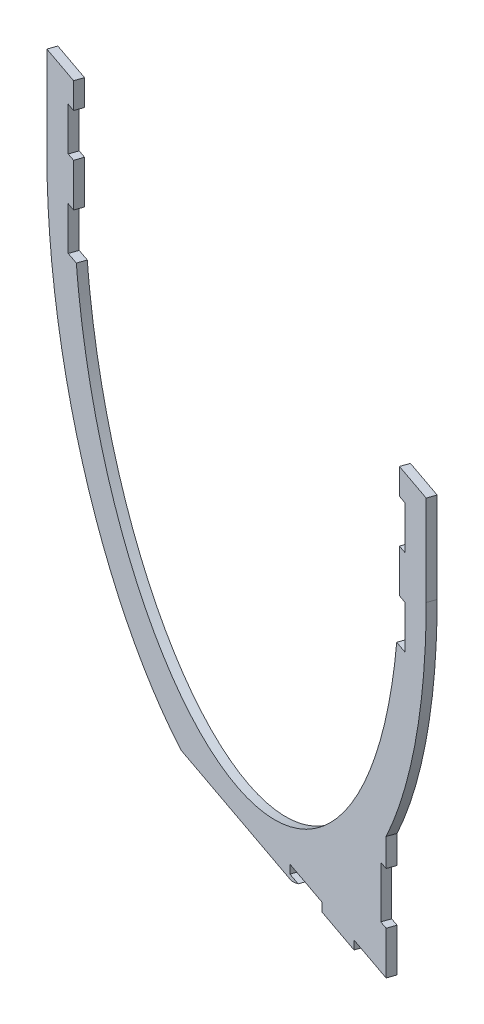
SolidWorks part; units mm, degrees
ref_plane "Front Plane" through (0, 0, 0) normal (0, 0, 1) x (1, 0, 0)
ref_plane "Top Plane" through (0, 0, 0) normal (0, 1, 0) x (1, 0, 0)
ref_plane "Right Plane" through (0, 0, 0) normal (1, 0, 0) x (0, 0, -1)
sketch "Sketch2" plane through (0, 0, 0) normal (0, 1, 0) x (1, 0, 0)
  line L0 (-295.0403, 95.1378) -> (-34.5174, 903.069) construction
  line L1 (-25, 910) -> (25, 910) construction
  line L2 (0, 0) -> (0, 870) construction
  line L3 (-181.6808, 251.1814) -> (-9.5174, 785.0928) construction
  line L4 (295.0403, 95.1378) -> (32.2825, 910) construction
  line L5 (181.6808, 251.1814) -> (9.5174, 785.0928) construction
  line L6 (-250, 0) -> (-250, 956.0819)
  line L7 (-250, 956.0819) -> (250, 783.9181)
  line L8 (-591.5307, 0) -> (570.3863, 0) construction
  line L9 (181.6808, -251.1814) -> (9.5174, -785.0928) construction
  line L10 (295.0403, -95.1378) -> (32.2825, -910) construction
  line L11 (-181.6808, -251.1814) -> (-9.5174, -785.0928) construction
  line L12 (-25, -910) -> (25, -910) construction
  line L13 (-295.0403, -95.1378) -> (-34.5174, -903.069) construction
  line L14 (250, 783.9181) -> (250, 0)
  line L15 (0, 870) -> (-535.6255, 184.4306)
  line L16 (250, 783.9181) -> (-338.6228, 30.5153)
  line L17 (-662.1318, 870) -> (570.3863, 870) construction
  line L18 (-338.6228, 30.5153) -> (-732.6282, 338.346)
  line L19 (-732.6282, 338.346) -> (-250, 956.0819)
  line L20 (0, 870) -> (-283.2443, 47.3988) construction
  circle A0 centre (0, 0) radius 250 construction
  arc A1 (181.6808, 251.1814) -> (-181.6808, 251.1814) centre (0, 0) ccw construction
  arc A2 (-9.5174, 785.0928) -> (9.5174, 785.0928) centre (0, 782.0238) cw construction
  arc A3 (-295.0403, 95.1378) -> (-295.0403, -95.1378) centre (0, 0) ccw construction
  arc A4 (-25, 910) -> (-34.5174, 903.069) centre (-25, 900) ccw construction
  arc A5 (25, 910) -> (34.5174, 903.069) centre (25, 900) cw construction
  arc A6 (0, 0) -> (-535.6255, 184.4306) centre (0, 870) cw construction
  arc A22 (25, -910) -> (34.5174, -903.069) centre (25, -900) ccw construction
  arc A23 (-25, -910) -> (-34.5174, -903.069) centre (-25, -900) cw construction
  arc A24 (-9.5174, -785.0928) -> (9.5174, -785.0928) centre (0, -782.0238) ccw construction
  arc A25 (181.6808, -251.1814) -> (-181.6808, -251.1814) centre (0, 0) cw construction
  arc A26 (-181.6808, -251.1814) -> (181.6808, -251.1814) centre (0, 0) ccw construction
  arc A27 (295.0403, -95.1378) -> (295.0403, 95.1378) centre (0, 0) ccw construction
  point P15 (0, 814.6081)
  point P17 (-32.2825, 910)
  point P21 (0, 910)
  point P69 (0, -910)
  dimension "D1" = 500
  dimension "D2" = 10
  dimension "D3" = 10
  dimension "D4" = 870
  dimension "D5" = 19
  dimension "D8" = 60
  dimension "D9" = 910
  dimension "D11" = 50
ref_plane "Plane1" through (0, 0, -870) normal (0, 0, 1) x (1, 0, 0)
sketch "Sketch3" plane through (0, 0, -870) normal (0, 0, 1) x (1, 0, 0)
  line L0 (0, 0) -> (0, 621.6859) construction
ref_plane "Plane2" through (267.8127, 0, -777.7847) normal (-0.3256, 0, 0.9455) x (0.9455, 0, 0.3256)
ref_plane "Plane3" through (274.3241, 0, -796.695) normal (-0.3256, 0, 0.9455) x (0.9455, 0, 0.3256)
sketch "Sketch4" plane through (274.3241, 0, -796.695) normal (-0.3256, 0, 0.9455) x (0.9455, 0, 0.3256)
  line L0 (-283.2443, 938.347) -> (-283.2443, -30) construction
  line L1 (-761.4579, 410) -> (151.8347, 410) construction
  line L2 (-538.2443, 410) -> (-538.2443, 470) construction
  line L3 (-538.2443, 470) -> (-558.2443, 470) construction
  line L4 (-558.2443, 470) -> (-558.2443, 350) construction
  line L5 (-558.2443, 470) -> (-544.8659, 527.0811) construction
  line L6 (-8.2443, 350) -> (-21.6227, 292.9189) construction
  line L7 (-558.2443, 350) -> (-544.8659, 292.9189) construction
  line L8 (-8.2443, 470) -> (-21.6227, 527.0811) construction
  line L9 (-8.2443, 470) -> (-8.2443, 350) construction
  line L10 (21.7557, 485) -> (21.7557, 515)
  line L11 (-386.784, -30) -> (-179.7046, -30)
  line L12 (21.7557, 515) -> (71.7557, 515)
  line L13 (-118.2838, 5.4462) -> (39.5332, 5.4462) construction
  line L14 (-118.2838, 17.9462) -> (-18.2838, 17.9462) construction
  line L15 (-118.2838, 17.9462) -> (-118.2838, -7.0538) construction
  line L16 (-118.2838, -7.0538) -> (-18.2838, -7.0538) construction
  line L17 (-18.2838, 17.9462) -> (-18.2838, -7.0538) construction
  line L18 (1.7557, 17.9462) -> (6.7557, 17.9462) construction
  line L19 (-63.2443, -15) -> (-3.2443, -15)
  line L20 (-3.2443, 155) -> (-13.2443, 155) construction
  line L21 (21.7557, 335) -> (31.7557, 335)
  line L22 (31.7557, 335) -> (31.7557, 485) construction
  line L23 (31.7557, 485) -> (21.7557, 485)
  line L24 (21.7557, 485) -> (21.7557, 335) construction
  line L25 (-3.2443, 155) -> (-3.2443, -25) construction
  line L26 (71.7557, 515) -> (71.7557, 410)
  line L27 (21.7557, 515) -> (21.7557, 485)
  line L28 (-8.2443, 470) -> (1.7557, 470) construction
  line L29 (1.7557, 470) -> (1.7557, 350) construction
  line L30 (1.7557, 350) -> (-8.2443, 350) construction
  line L31 (1.7557, 470) -> (1.7557, 485) construction
  line L32 (1.7557, 485) -> (6.7557, 485) construction
  line L33 (6.7557, 485) -> (6.7557, -7.0538) construction
  line L34 (1.7557, 350) -> (1.7557, -7.0538) construction
  line L35 (1.7557, -7.0538) -> (6.7557, -7.0538) construction
  line L36 (-3.2443, -25) -> (-13.2443, -25) construction
  line L37 (-13.2443, 155) -> (-13.2443, -25) construction
  line L38 (-183.2443, -15) -> (-3.2443, -15) construction
  line L39 (-183.2443, -15) -> (-183.2443, -25)
  line L40 (-183.2443, -25) -> (-3.2443, -25) construction
  line L41 (-3.2443, -15) -> (-3.2443, -25) construction
  line L42 (-3.2443, 35) -> (-3.2443, -15)
  line L43 (-123.2443, -15) -> (-123.2443, -25)
  line L44 (-63.2443, -25) -> (-63.2443, -15)
  line L45 (-13.2443, 35) -> (-3.2443, 35)
  line L46 (-13.2443, 95) -> (-3.2443, 95)
  line L47 (-3.2443, 95) -> (-3.2443, 127.2211)
  line L48 (-13.2443, 95) -> (-13.2443, 35)
  line L49 (-3.2443, 35) -> (-3.2443, -25) construction
  line L50 (-3.2443, -15) -> (32.7751, -15.846)
  line L51 (-123.2443, -25) -> (-63.2443, -25)
  line L52 (-123.2443, -15) -> (-183.2443, -15)
  line L53 (-183.2443, -25) -> (-167.8054, -25)
  line L54 (31.7557, 435) -> (21.7557, 435)
  line L55 (31.7557, 385) -> (21.7557, 385)
  line L56 (31.7557, 435) -> (31.7557, 485)
  line L57 (21.7557, 435) -> (21.7557, 385)
  line L58 (31.7557, 385) -> (31.7557, 335)
  line L59 (21.7557, 335) -> (16.6093, 335)
  line L60 (-638.2443, 515) -> (-638.2443, 410)
  line L61 (-588.2443, 515) -> (-638.2443, 515)
  line L62 (-598.2443, 485) -> (-588.2443, 485)
  line L63 (-598.2443, 435) -> (-598.2443, 485)
  line L64 (-598.2443, 435) -> (-588.2443, 435)
  line L65 (-598.2443, 385) -> (-588.2443, 385)
  line L66 (-588.2443, 435) -> (-588.2443, 385)
  line L67 (-598.2443, 385) -> (-598.2443, 335)
  line L68 (-588.2443, 335) -> (-583.0979, 335)
  line L69 (-588.2443, 335) -> (-598.2443, 335)
  line L70 (-588.2443, 485) -> (-588.2443, 515)
  ellipse E0 centre (-283.2443, 410) end of major axis (-283.2443, 55) minor radius 250 construction
  ellipse E1 centre (-283.2443, 410) end of major axis (-283.2443, 790) minor radius 275 construction
  ellipse E2 centre (-283.2443, 410) end of major axis (-283.2443, 788.3034) minor radius 275.1297 (-544.8659, 527.0811) -> (-21.6227, 527.0811) cw construction
  ellipse E3 centre (-283.2443, 410) end of major axis (-283.2443, 31.6966) minor radius 275.1297 (-544.8659, 292.9189) -> (-21.6227, 292.9189) ccw construction
  ellipse E4 centre (-283.2443, 410) end of major axis (-283.2443, 0) minor radius 305 (-588.2443, 410) -> (21.7557, 410) ccw construction
  ellipse E5 centre (-283.2443, 410) end of major axis (-283.2443, 870) minor radius 355 (-638.2443, 410) -> (-386.784, -30) ccw
  ellipse E6 centre (-283.2443, 410) end of major axis (-283.2443, -25) minor radius 332.1412 (48.8969, 410) -> (-283.2443, -25) cw construction
  ellipse E7 centre (-283.2443, 410) end of major axis (-283.2443, 870) minor radius 355 (-3.2443, 127.2211) -> (71.7557, 410) ccw
  ellipse E8 centre (-283.2443, 410) end of major axis (-283.2443, 870) minor radius 355 (-179.7046, -30) -> (-167.8054, -25) ccw
  ellipse E9 centre (-283.2443, 410) end of major axis (-283.2443, 0) minor radius 305 (16.6093, 335) -> (-583.0979, 335) cw
  point P26 (-8.2443, 410)
  point P31 (-558.2443, 410)
  dimension "D1" = 500
  dimension "D2" = 710
  dimension "D3" = 550
  dimension "D4" = 760
  dimension "D5" = 20
  dimension "D6" = 60
  dimension "D7" = 30
  dimension "D8" = 30
  dimension "D9" = 30
  dimension "D10" = 25
  dimension "D11" = 50
  dimension "D12" = 50
  dimension "D13" = 100
  dimension "D14" = 10
  dimension "D15" = 10
  dimension "D16" = 10
  dimension "D17" = 150
  dimension "D18" = 75
  dimension "D19" = 25
  dimension "D20" = 10
  dimension "D21" = 5
  dimension "D22" = 180
  dimension "D23" = 60
  dimension "D24" = 60
  dimension "D25" = 280
  dimension "D26" = 5
  dimension "D27" = 180
  dimension "D28" = 60
  dimension "D29" = 60
  dimension "D30" = 25
  dimension "D31" = 105
extrude "Boss-Extrude1" add sketch "Sketch4" along normal blind 10 contours L59 E9 L68 L69 L67 L65 L66 L64 L63 L62 L70 L61 L60 E5 L11 E8 L53 L39 L52 L43 L51 L44 L19 L42 L45 L48 L46 L47 E7 L26 L12 L10 L23 L56 L54 L57 L55 L58 L21
